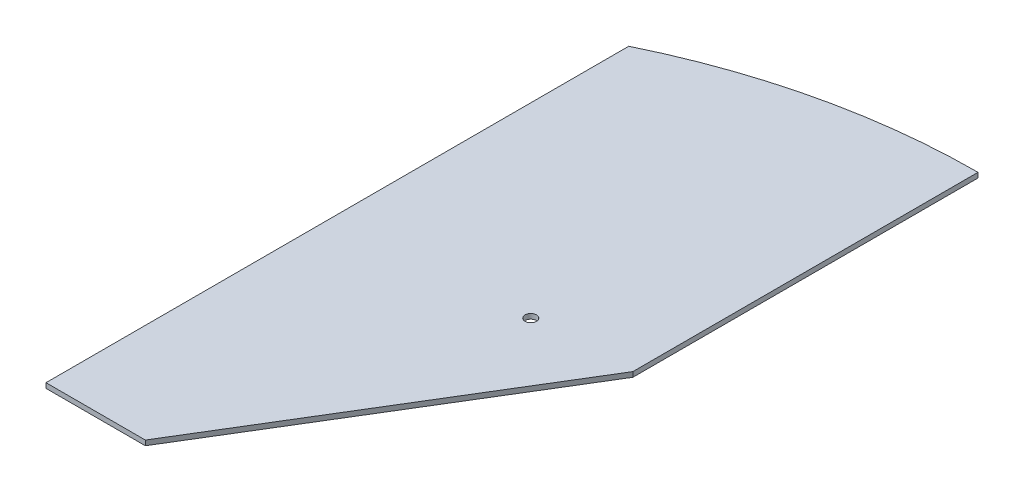
SolidWorks part; units mm, degrees
ref_plane "Front Plane" through (0, 0, 0) normal (0, 0, 1) x (1, 0, 0)
ref_plane "Top Plane" through (0, 0, 0) normal (0, 1, 0) x (1, 0, 0)
ref_plane "Right Plane" through (0, 0, 0) normal (1, 0, 0) x (0, 0, -1)
sketch "Sketch1" plane through (0, 0, 0) normal (0, 1, 0) x (1, 0, 0)
  line L0 (-0.8458, -19.2201) -> (12.1542, 2.134)
  line L3 (-0.8458, -19.2201) -> (-7.8458, -19.2201)
  line L4 (-7.8458, 21.8456) -> (-7.8458, -19.2201)
  line L5 (12.1542, 2.134) -> (12.1542, 26.4569)
  arc A0 (12.1542, 26.4569) -> (-7.8458, 21.8456) centre (12.1542, -19.2201) ccw
  point P0 (0, 0)
  point P4 (5.6542, -8.5431)
  dimension "D4" = 7
  dimension "D2" = 20
  dimension "D1" = 24.3229
  dimension "D3" = 25
  dimension "D5" = 35
  dimension "D6" = 41.0657
extrude "Boss-Extrude1" add sketch "Sketch1" along normal blind 0.35
scale "Scale1" scale about centroid uniform scaling yes scale factor 10
sketch "Sketch2" plane through (0, 1.925, 0) normal (0, 1, 0) x (1, 0, 0)
  line L0 (109.8548, -29.7379) -> (43.3548, -29.7379) construction
  line L1 (-20.1768, -243.3314) -> (109.8232, -29.7898) construction
  circle A0 centre (41.2165, -33.1183) radius 4
  dimension "D1" = 66.5
  dimension "D2" = 4
extrude "Cut-Extrude1" cut sketch "Sketch2" against normal through all both and the other way through all
